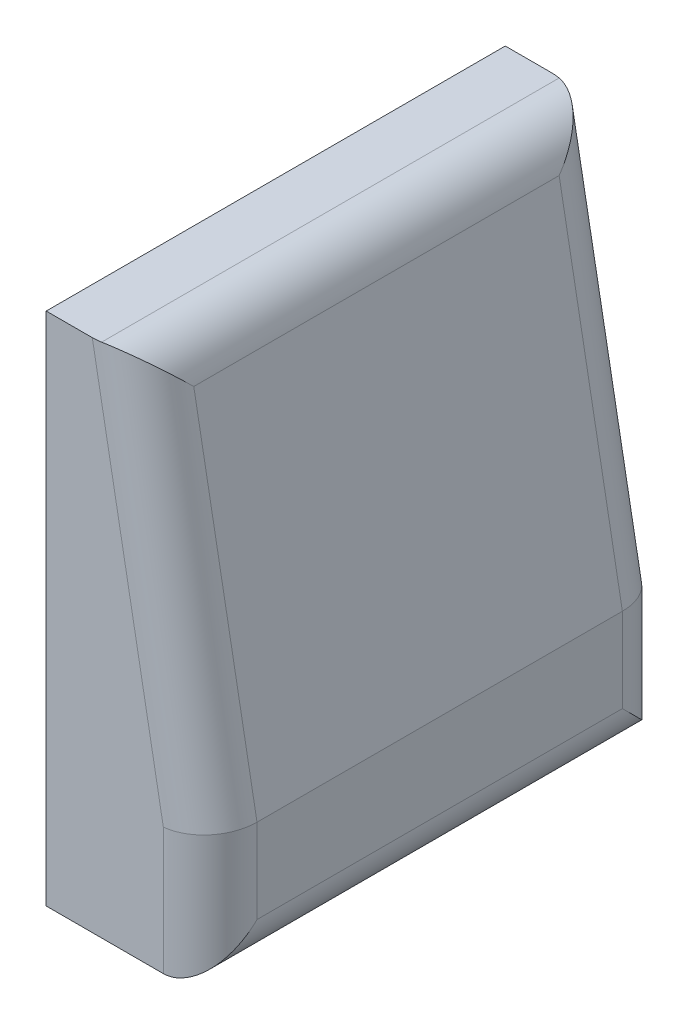
SolidWorks part; units mm, degrees
ref_plane "Front Plane" through (0, 0, 0) normal (0, 0, 1) x (1, 0, 0)
ref_plane "Top Plane" through (0, 0, 0) normal (0, 1, 0) x (1, 0, 0)
ref_plane "Right Plane" through (0, 0, 0) normal (1, 0, 0) x (0, 0, -1)
sketch "Sketch1" plane through (0, 0, 0) normal (0, 0, 1) x (1, 0, 0)
  line L0 (0, 0) -> (0, 1100)
  line L1 (0, 1100) -> (200, 1100)
  line L2 (200, 1100) -> (350, 280)
  line L4 (350, 0) -> (0, 0)
  line L5 (350, 280) -> (350, 0)
  dimension "D2" = 200
  dimension "D3" = 350
  dimension "D1" = 1100
  dimension "D6" = 280
extrude "Boss-Extrude1" add sketch "Sketch1" along normal mid plane 980
fillet "Fillet3" radius 100 6 edges at (275, 690, 490) (200, 1100, 0) (275, 690, -490) (350, 0, 0) (350, 140, 490) (350, 140, -490)
